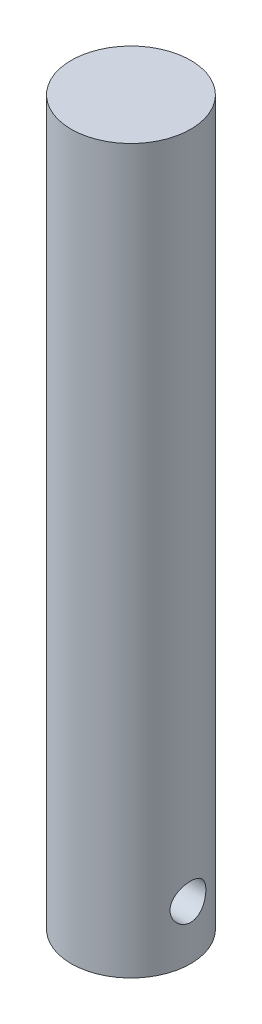
SolidWorks part; units mm, degrees
ref_plane "Alzado" through (0, 0, 0) normal (0, 0, 1) x (1, 0, 0)
ref_plane "Planta" through (0, 0, 0) normal (0, 1, 0) x (1, 0, 0)
ref_plane "Vista lateral" through (0, 0, 0) normal (1, 0, 0) x (0, 0, -1)
sketch "Croquis1" plane through (0, 0, 0) normal (0, 1, 0) x (1, 0, 0)
  circle A0 centre (0, 0) radius 10
  dimension "D1" = 20
extrude "Saliente-Extruir1" add sketch "Croquis1" along normal blind 100 and the other way blind 21
sketch "Croquis2" plane through (0, 0, 0) normal (1, 0, 0) x (0, 0, -1)
  line L0 (-10, -21) -> (10, -21) construction
  circle A0 centre (0, -12) radius 3
  dimension "D1" = 6
  dimension "D2" = 9
extrude "Cortar-Extruir1" cut sketch "Croquis2" against normal mid plane 25
